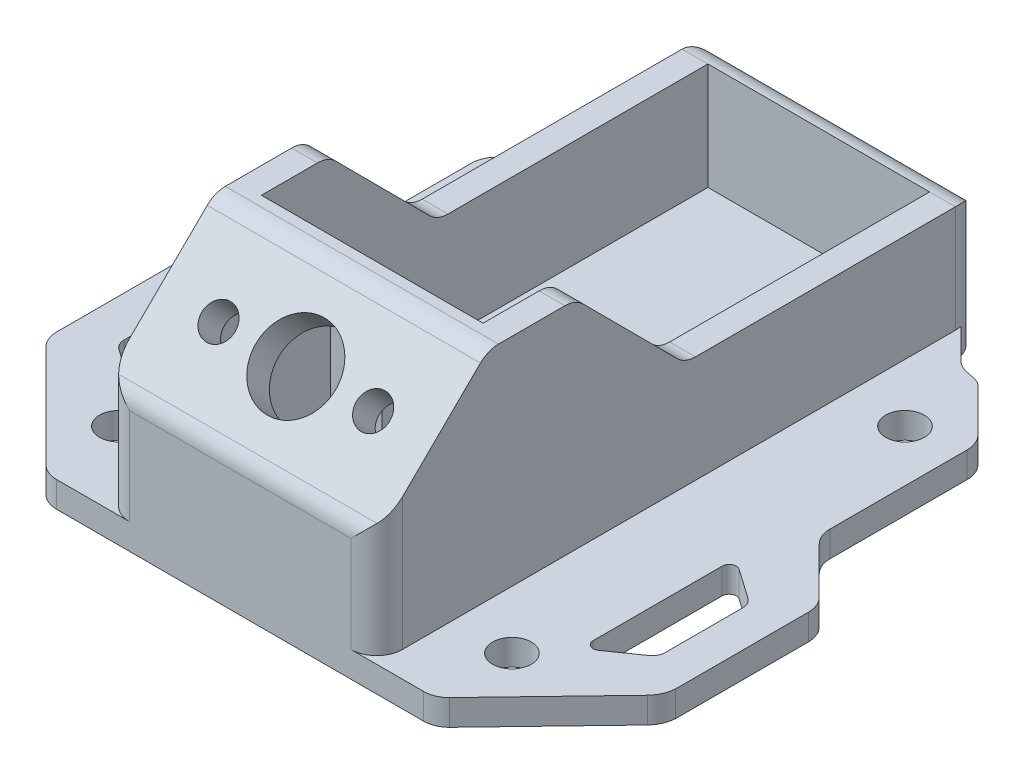
SolidWorks part; units mm, degrees
other "Markup1"
sketch "Sketch8" plane through (-24.0919, 18.8, -23.613) normal (-0.1424, 0.3442, -0.928) x (-0.9891, -0.013, 0.147)
ref_plane "Front Plane" through (0, 0, 0) normal (0, 0, 1) x (1, 0, 0)
ref_plane "Top Plane" through (0, 0, 0) normal (0, 1, 0) x (1, 0, 0)
ref_plane "Right Plane" through (0, 0, 0) normal (1, 0, 0) x (0, 0, -1)
sketch "Sketch1" plane through (0, 0, 0) normal (0, 1, 0) x (1, 0, 0)
  line L0 (8.6658, -21.287) -> (-8.5342, -21.287) construction
  line L3 (-8.5342, -7.687) -> (-4.3142, -7.687) construction
  line L4 (8.6658, -7.687) -> (4.4458, -7.687) construction
  line L5 (4.4458, -7.687) -> (4.0658, -3.875) construction
  line L6 (-4.3142, -7.687) -> (-3.9342, -3.875) construction
  line L7 (4.0658, -3.875) -> (-3.9342, -3.875) construction
  line L8 (0.0658, 23.613) -> (0.0658, -23.287) construction
  line L9 (-8.5342, -7.687) -> (-8.5342, -21.287) construction
  line L10 (18.5724, 15.4556) -> (15.4008, 18.6272)
  line L11 (8.6658, -7.687) -> (8.6658, -21.287) construction
  line L12 (23.9081, -3.0223) -> (23.9081, -13.3283)
  line L14 (-14.1703, -23.287) -> (14.3019, -23.287)
  line L17 (23.3223, -1.6081) -> (19.7439, 1.9704)
  line L18 (19.1581, 3.3846) -> (19.1581, 14.0414)
  line L19 (-19.3419, 14.0414) -> (-19.3419, 3.3846)
  line L20 (-24.0919, -3.0223) -> (-24.0919, -13.3654)
  line L21 (8.4998, 23.613) -> (-8.3682, 23.613)
  line L35 (-15.5845, -22.7012) -> (-23.5061, -14.7796)
  line L36 (-23.5061, -1.6081) -> (-19.9276, 1.9704)
  line L37 (-18.7561, 15.4556) -> (-15.5845, 18.6272)
  line L38 (-13.1229, 19.7819) -> (-9.945, 22.9599)
  line L39 (-14.6946, 19.1431) -> (-14.0129, 19.2661)
  line L40 (9.5383, 23.1829) -> (12.9392, 19.7819)
  line L41 (13.8292, 19.2661) -> (14.5108, 19.1431)
  line L42 (15.7161, -22.7012) -> (23.2379, -14.863)
  circle A0 centre (-15.3419, -17.287) radius 1.5 construction
  circle A1 centre (15.1581, -17.287) radius 1.5 construction
  circle A2 centre (15.1581, 13.213) radius 1.5 construction
  circle A3 centre (-15.3419, 13.213) radius 1.5 construction
  arc A4 (-9.945, 22.9599) -> (-8.3682, 23.613) centre (-8.3682, 21.3831) cw
  arc A5 (8.4998, 23.613) -> (9.5383, 23.1829) centre (8.4998, 22.1444) cw
  arc A6 (12.9392, 19.7819) -> (13.8292, 19.2661) centre (14.3534, 21.1962) ccw
  arc A7 (14.5108, 19.1431) -> (15.4008, 18.6272) centre (14.2421, 17.6538) cw
  arc A8 (-13.1229, 19.7819) -> (-14.0129, 19.2661) centre (-14.5372, 21.1962) cw
  arc A9 (-14.6946, 19.1431) -> (-15.5845, 18.6272) centre (-14.4258, 17.6538) ccw
  arc A10 (-18.7561, 15.4556) -> (-19.3419, 14.0414) centre (-17.3419, 14.0414) ccw
  arc A11 (-19.3419, 3.3846) -> (-19.9276, 1.9704) centre (-21.3419, 3.3846) cw
  arc A12 (-23.5061, -1.6081) -> (-24.0919, -3.0223) centre (-22.0919, -3.0223) ccw
  arc A13 (-24.0919, -13.3654) -> (-23.5061, -14.7796) centre (-22.0919, -13.3654) ccw
  arc A14 (-15.5845, -22.7012) -> (-14.1703, -23.287) centre (-14.1703, -21.287) ccw
  arc A15 (14.3019, -23.287) -> (15.7161, -22.7012) centre (14.3019, -21.287) ccw
  arc A16 (23.2379, -14.863) -> (23.9081, -13.3283) centre (21.4907, -13.1863) ccw
  arc A17 (23.3223, -1.6081) -> (23.9081, -3.0223) centre (21.9081, -3.0223) cw
  arc A18 (19.7439, 1.9704) -> (19.1581, 3.3846) centre (21.1581, 3.3846) cw
  arc A19 (18.5724, 15.4556) -> (19.1581, 14.0414) centre (17.1582, 14.0414) cw
  point P66 (4.6681, -7.687)
  point P67 (4.2881, -3.687)
  point P68 (-3.3319, -3.1865)
  point P69 (0, 0)
  point P70 (-3.3319, -7.687)
  point P71 (-3.3319, -7.687)
  point P72 (0, 0)
  point P73 (0, 0)
  point P74 (0, 0)
  point P75 (-4.0918, -3.875)
  point P76 (-4.4699, -7.687)
  point P77 (4.3406, -7.687)
  dimension "D1" = 8
  dimension "D3" = 4.22
  dimension "D4" = 13.6
  dimension "D5" = 17.2
  dimension "D6" = 2
extrude "Boss-Extrude1" add sketch "Sketch1" along normal blind 2
sketch "Sketch2" plane through (0, 2, 0) normal (0, 1, 0) x (1, 0, 0)
  circle A0 centre (-15.3419, -17.287) radius 1.5 construction
  circle A1 centre (15.1581, -17.287) radius 1.5 construction
  circle A2 centre (15.1581, 13.213) radius 1.5 construction
  circle A3 centre (-15.3419, 13.213) radius 1.5 construction
  circle A4 centre (-15.3419, -17.287) radius 1.5
  circle A5 centre (15.1581, -17.287) radius 1.5
  circle A6 centre (15.1581, 13.213) radius 1.5
  circle A7 centre (-15.3419, 13.213) radius 1.5
extrude "Cut-Extrude1" cut sketch "Sketch2" against normal through all
sketch "Sketch3" plane through (0, 0, 0) normal (0, -1, 0) x (1, 0, 0)
  line L42 (18.3323, 13.7381) -> (20.6259, 12.132)
  line L43 (0.0658, 23.287) -> (0.0658, -23.613) construction
  line L44 (-14.1703, 23.287) -> (14.3019, 23.287) construction
  line L49 (8.4998, -23.613) -> (-8.3682, -23.613) construction
  line L50 (-17.3342, 13.287) -> (-17.3342, 3.287)
  line L51 (-18.2007, 2.8359) -> (-20.4943, 4.442)
  line L53 (-20.9342, 5.287) -> (-20.9342, 11.287)
  line L54 (-20.9342, 8.287) -> (-17.3342, 8.287) construction
  line L55 (-18.2007, 13.7381) -> (-20.4943, 12.132)
  line L56 (-14.1703, 23.287) -> (14.3019, 23.287) construction
  line L57 (21.0658, 5.287) -> (21.0658, 11.287)
  line L58 (18.3323, 2.8359) -> (20.6259, 4.442)
  line L59 (17.4658, 13.287) -> (17.4658, 3.287)
  arc A9 (-18.2007, 2.8359) -> (-17.3342, 3.287) centre (-17.8848, 3.287) ccw
  arc A12 (-20.9342, 5.287) -> (-20.4943, 4.442) centre (-19.9026, 5.287) ccw
  arc A13 (-18.2007, 13.7381) -> (-17.3342, 13.287) centre (-17.8848, 13.287) cw
  arc A14 (-20.9342, 11.287) -> (-20.4943, 12.132) centre (-19.9026, 11.287) cw
  arc A15 (21.0658, 11.287) -> (20.6259, 12.132) centre (20.0342, 11.287) ccw
  arc A16 (18.3323, 13.7381) -> (17.4658, 13.287) centre (18.0165, 13.287) ccw
  arc A17 (21.0658, 5.287) -> (20.6259, 4.442) centre (20.0342, 5.287) cw
  arc A18 (18.3323, 2.8359) -> (17.4658, 3.287) centre (18.0165, 3.287) cw
  point P31 (0, 0)
  dimension "D5" = 3.6
  dimension "D6" = 10
  dimension "D8" = 6
  dimension "D9" = 125
  dimension "D11" = 2.8
  dimension "D12" = 17.4
  dimension "D14" = 10
extrude "Cut-Extrude3" cut sketch "Sketch3" against normal through all
sketch "Sketch4" plane through (0, 2, 0) normal (0, 1, 0) x (1, 0, 0)
  line L0 (0.0658, 23.613) -> (0.0658, -23.287) construction
  line L1 (8.4998, 23.613) -> (-8.3682, 23.613) construction
  line L2 (-14.1703, -23.287) -> (14.3019, -23.287) construction
  line L3 (-8.5342, -21.287) -> (-8.5342, 21.613)
  line L4 (-8.5342, -23.287) -> (8.6658, -23.287)
  line L5 (-10.5342, -21.287) -> (-10.5342, 21.613)
  line L6 (-8.5342, 23.613) -> (8.6658, 23.613)
  line L7 (10.6658, -21.287) -> (10.6658, 21.613)
  line L8 (-8.5342, 21.613) -> (8.6658, 21.613)
  line L9 (8.6658, -21.287) -> (8.6658, 21.613)
  line L10 (-8.5342, -21.287) -> (8.6658, -21.287)
  line L11 (-10.5342, -23.287) -> (10.6658, -23.287) construction
  line L12 (-10.5342, -23.287) -> (-10.5342, 23.613) construction
  line L13 (10.6658, -23.287) -> (10.6658, 23.613) construction
  line L14 (-10.5342, 23.613) -> (10.6658, 23.613) construction
  arc A0 (-8.5342, -23.287) -> (-10.5342, -21.287) centre (-8.5342, -21.287) cw
  arc A1 (8.6658, -23.287) -> (10.6658, -21.287) centre (8.6658, -21.287) ccw
  arc A2 (8.6658, 23.613) -> (10.6658, 21.613) centre (8.6658, 21.613) cw
  arc A3 (-10.5342, 21.613) -> (-8.5342, 23.613) centre (-8.5342, 21.613) cw
  point P17 (-10.5342, -23.287)
  dimension "D3" = 2
  dimension "D1" = 21.2
  dimension "D4" = 17.2
  dimension "D5" = 2
  dimension "D2" = 2
extrude "Boss-Extrude2" add sketch "Sketch4" along normal blind 16.8 and the other way up to surface (2 mm away) other way up to face at (19.3641, 0, 8.287)
sketch "Sketch5" plane through (-10.5342, 0, 0) normal (-1, 0, 0) x (0, 0, 1)
  line L0 (-21.613, 10.3) -> (-1.4435, 10.3)
  line L1 (-23.613, 0) -> (-23.613, 18.8) construction
  line L2 (-0.0268, 10.8882) -> (7.2713, 18.2118)
  line L3 (-21.613, 18.8) -> (21.287, 18.8) construction
  line L4 (8.688, 18.8) -> (13.838, 18.8)
  line L5 (15.2414, 18.2249) -> (22.6905, 10.8876)
  line L8 (26.0983, 6.8834) -> (26.0983, 23.7713)
  line L9 (26.0983, 23.7713) -> (-26.1571, 23.7713)
  line L10 (-26.1571, 23.7713) -> (-26.1571, 6.54)
  line L12 (23.287, 2) -> (23.287, 18.8) construction
  line L13 (23.287, 9.4627) -> (23.287, 6.8834)
  line L14 (23.287, 6.8834) -> (26.0983, 6.8834)
  line L15 (-23.613, 8.3) -> (-23.613, 6.54)
  line L16 (-23.613, 6.54) -> (-26.1571, 6.54)
  arc A0 (7.2713, 18.2118) -> (8.688, 18.8) centre (8.688, 16.8) cw
  arc A1 (13.838, 18.8) -> (15.2414, 18.2249) centre (13.838, 16.8) cw
  arc A2 (22.6905, 10.8876) -> (23.287, 9.4627) centre (21.287, 9.4627) cw
  arc A3 (-1.4435, 10.3) -> (-0.0268, 10.8882) centre (-1.4435, 12.3) ccw
  arc A4 (-21.613, 10.3) -> (-23.613, 8.3) centre (-21.613, 8.3) ccw
  point P10 (-26.317, 6.54)
  point P20 (7.8575, 18.8)
  point P23 (14.6575, 18.8)
  point P26 (23.287, 10.3)
  point P29 (-0.613, 10.3)
  point P32 (-23.613, 10.3)
  dimension "D4" = 2
  dimension "D1" = 23
  dimension "D2" = 6.8
  dimension "D3" = 12
  dimension "D5" = 8.5
extrude "Cut-Extrude4" cut sketch "Sketch5" against normal through all
sketch "Sketch6" plane through (8.6658, 0, 0) normal (-1, 0, 0) x (0, 0, 1)
  line L0 (21.287, 12.27) -> (15.2414, 18.2249) construction
  line L1 (21.287, 12.27) -> (15.2414, 18.2249)
  line L2 (13.838, 18.8) -> (13.0348, 18.8)
  line L3 (13.838, 18.8) -> (8.688, 18.8) construction
  line L4 (13.0348, 18.8) -> (13.0348, 16.8893)
  line L5 (13.0348, 16.8893) -> (21.3136, 8.7347)
  line L6 (21.3136, 8.7347) -> (23.287, 8.7347)
  line L7 (23.287, 2) -> (23.287, 9.4627) construction
  line L8 (23.287, 8.7347) -> (23.287, 9.4627)
  line L9 (21.287, 12.27) -> (22.6905, 10.8876)
  arc A0 (15.2414, 18.2249) -> (13.838, 18.8) centre (13.838, 16.8) ccw construction
  arc A1 (15.2414, 18.2249) -> (13.838, 18.8) centre (13.838, 16.8) ccw
  arc A2 (23.287, 9.4627) -> (22.6905, 10.8876) centre (21.287, 9.4627) ccw construction
  arc A3 (23.287, 9.4627) -> (22.6905, 10.8876) centre (21.287, 9.4627) ccw
  dimension "D1" = 2.5
extrude "Boss-Extrude3" add sketch "Sketch6" along normal up to next
sketch "Sketch7" plane through (0, 16.87, 16.6169) normal (0, 0.7124, 0.7017) x (1, 0, 0)
  line L0 (0.0658, 1.9307) -> (0.0658, -8.5251) construction
  line L1 (10.6658, 1.9307) -> (-10.5342, 1.9307) construction
  line L2 (10.0907, -8.5251) -> (-9.959, -8.5251) construction
  line L3 (-10.5342, -3.2972) -> (10.6658, -3.2972) construction
  line L4 (-10.5342, 1.9307) -> (-10.5342, -6.5551) construction
  line L5 (10.6658, 16.8012) -> (10.6658, -13.762) construction
  circle A0 centre (0.0658, -3.2972) radius 3.1
  circle A1 centre (6.0658, -3.2972) radius 1.3
  circle A2 centre (-5.9342, -3.2972) radius 1.3
  dimension "D1" = 2.6
  dimension "D2" = 6.2
  dimension "D3" = 6
extrude "Cut-Extrude5" cut sketch "Sketch7" against normal up to next
sketch "Sketch9" plane through (0, 2, 0) normal (0, 1, 0) x (1, 0, 0)
  line L0 (-8.5342, -21.287) -> (8.6658, -21.287)
  line L1 (8.6658, -21.287) -> (8.6658, -7.687)
  line L2 (8.6658, 21.613) -> (8.6658, -21.287) construction
  line L3 (8.6658, -7.687) -> (4.6658, -7.687)
  line L4 (4.6658, -7.687) -> (4.6658, -2.4921)
  line L5 (4.6658, -2.4921) -> (-4.5342, -2.4921)
  line L6 (-4.5342, -2.4921) -> (-4.5342, -7.687)
  line L7 (-4.5342, -7.687) -> (-8.5342, -7.687)
  line L8 (-8.5342, -21.287) -> (-8.5342, 21.613) construction
  line L9 (-8.5342, -7.687) -> (-8.5342, -21.287)
  line L10 (0.0658, -21.287) -> (0.0658, 21.613) construction
  line L11 (-8.5342, 21.613) -> (8.6658, 21.613) construction
  dimension "D1" = 4
  dimension "D3" = 13.6
extrude "Cut-Extrude6" cut sketch "Sketch9" against normal up to next
sketch "Sketch10" plane through (0, 2, 0) normal (0, 1, 0) x (1, 0, 0)
  line L0 (8.6658, -7.2713) -> (8.6658, 0.0268) construction
  line L1 (4.6658, -7.687) -> (8.6658, -7.687)
  line L2 (4.6658, -7.687) -> (4.6658, -5.287)
  line L3 (4.6658, -5.287) -> (8.6658, -5.287)
  line L4 (8.6658, -7.687) -> (8.6658, -5.287)
  line L5 (-8.5342, 0.0268) -> (-8.5342, -7.2713) construction
  line L6 (-4.5342, -7.687) -> (-8.5342, -7.687)
  line L7 (-4.5342, -7.687) -> (-4.5342, -5.287)
  line L8 (-4.5342, -5.287) -> (-8.5342, -5.287)
  line L9 (-8.5342, -7.687) -> (-8.5342, -5.287)
  dimension "D1" = 2.4
extrude "Boss-Extrude4" add sketch "Sketch10" along normal blind 8
